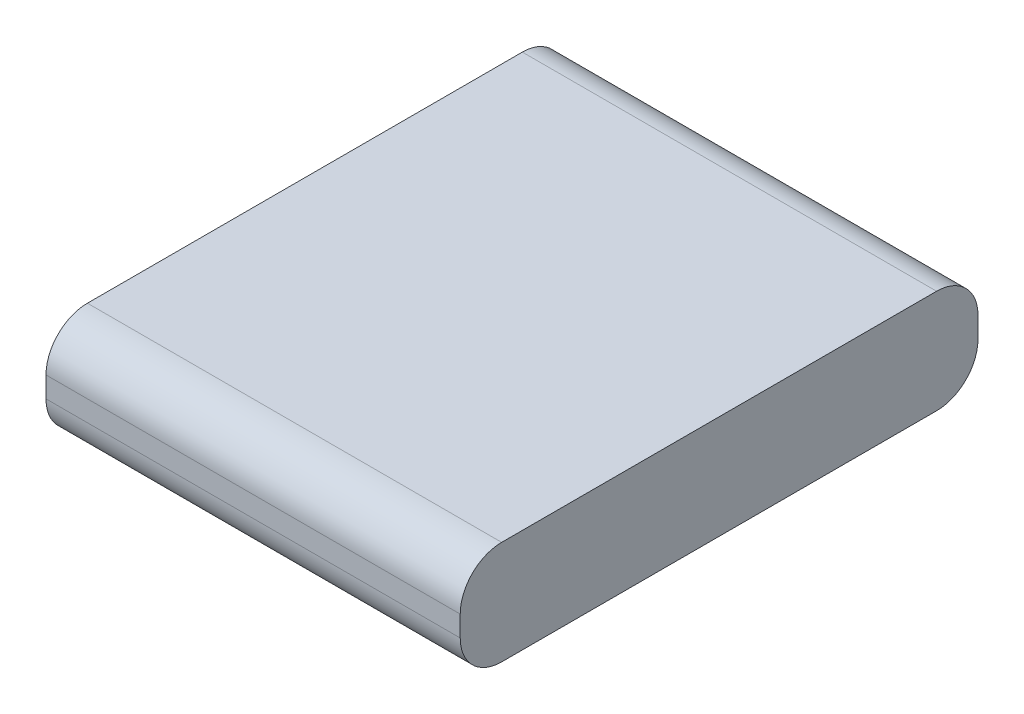
SolidWorks part; units mm, degrees
ref_plane "Front Plane" through (0, 0, 0) normal (0, 0, 1) x (1, 0, 0)
ref_plane "Top Plane" through (0, 0, 0) normal (0, 1, 0) x (1, 0, 0)
ref_plane "Right Plane" through (0, 0, 0) normal (1, 0, 0) x (0, 0, -1)
sketch "Sketch1" plane through (0, 0, 0) normal (0, 0, 1) x (1, 0, 0)
  line L1 (0, 0) -> (400, 0)
  line L2 (0, 0) -> (0, -100)
  line L3 (0, -100) -> (400, -100)
  line L4 (400, 0) -> (400, -100)
  dimension "D1" = 400
  dimension "D2" = 100
extrude "Boss-Extrude1" add sketch "Sketch1" along normal blind 500
fillet "Fillet2" radius 40 4 edges at (200, -100, 0) (200, 0, 0) (200, -100, 500) (200, 0, 500)
